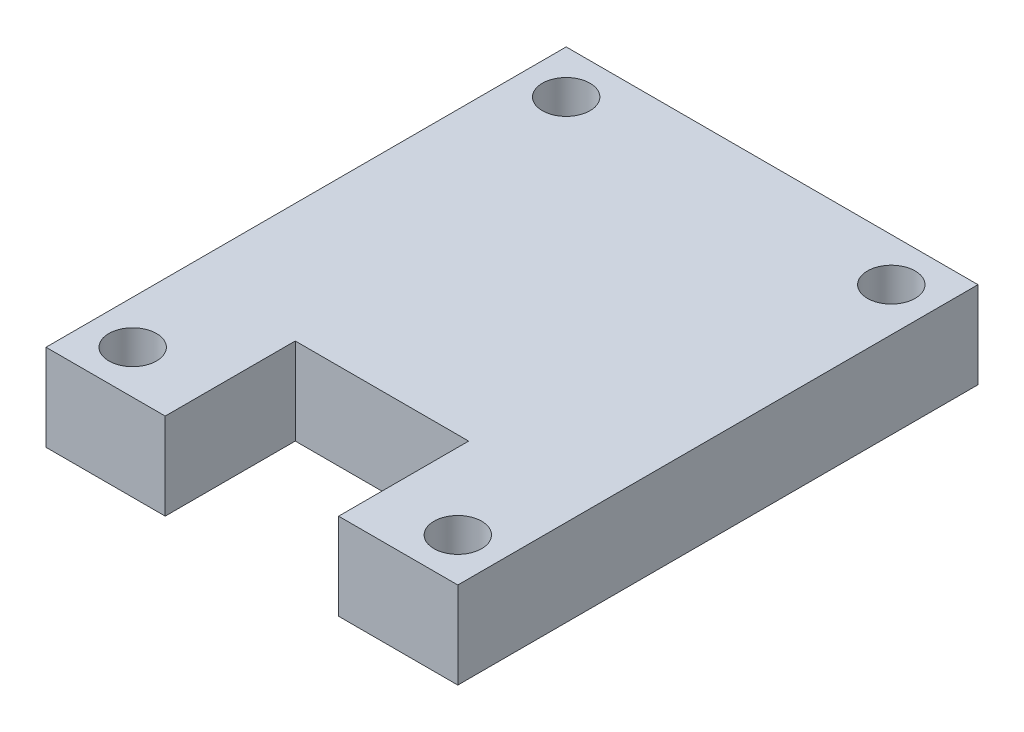
SolidWorks part; units mm, degrees
ref_plane "Plan de face" through (0, 0, 0) normal (0, 0, 1) x (1, 0, 0)
ref_plane "Plan de dessus" through (0, 0, 0) normal (0, 1, 0) x (1, 0, 0)
ref_plane "Plan de droite" through (0, 0, 0) normal (1, 0, 0) x (0, 0, -1)
sketch "Esquisse1" plane through (0, 0, 0) normal (0, 1, 0) x (1, 0, 0)
  line L0 (0, 0) -> (38, 0)
  line L1 (38, 0) -> (38, 48)
  line L2 (38, 48) -> (0, 48)
  line L3 (0, 48) -> (0, 0)
extrude "Boss.-Extru.1" add sketch "Esquisse1" along normal blind 8
sketch "Esquisse3" plane through (0, 0, 0) normal (0, -1, 0) x (1, 0, 0)
  line L0 (0, 0) -> (8, 0) construction
  line L1 (0, 0) -> (38, 0) construction
  line L2 (8, 0) -> (8, -8) construction
  line L3 (8, -8) -> (0, 0) construction
  line L4 (0, 0) -> (8, 0) construction
  line L5 (8, 0) -> (0, -8) construction
  line L6 (0, -48) -> (0, 0) construction
  line L7 (0, -8) -> (0, -48) construction
  line L8 (38, -48) -> (0, -48) construction
  line L9 (0, -48) -> (8, -48) construction
  line L10 (8, -48) -> (8, -40) construction
  line L11 (8, -40) -> (0, -48) construction
  line L12 (0, -48) -> (8, -48) construction
  line L13 (8, -48) -> (0, -40) construction
  line L14 (38, 0) -> (38, -8) construction
  line L15 (38, 0) -> (38, -48) construction
  line L16 (38, -8) -> (30, -8) construction
  line L17 (30, -8) -> (30, 0) construction
  line L18 (30, -8) -> (38, 0) construction
  line L19 (38, 0) -> (30, 0) construction
  line L20 (30, 0) -> (38, -8) construction
  line L21 (38, -8) -> (38, -48) construction
  line L22 (38, -48) -> (30, -48) construction
  line L23 (30, -48) -> (30, -40) construction
  line L24 (30, -40) -> (38, -48) construction
  line L25 (38, -48) -> (30, -48) construction
  line L26 (30, -48) -> (38, -40) construction
  line L27 (38, -40) -> (30, -40) construction
  circle A0 centre (4, -4) radius 2.2
  circle A1 centre (34, -4) radius 2.2
  circle A2 centre (34, -44) radius 2.2
  circle A3 centre (4, -44) radius 2.2
extrude "Enlèv. mat.-Extru.1" cut sketch "Esquisse3" against normal blind 8
sketch "Esquisse5" plane through (0, 8, 0) normal (0, 1, 0) x (1, 0, 0)
  line L0 (0, 0) -> (38, 0) construction
  line L1 (38, 0) -> (19, 0) construction
  line L2 (19, 0) -> (19, 12) construction
  line L3 (19, 12) -> (27, 12)
  line L4 (27, 12) -> (27, 0)
  line L5 (27, 0) -> (11, 0)
  line L6 (11, 0) -> (11, 12)
  line L7 (11, 12) -> (19, 12)
extrude "Enlèv. mat.-Extru.2" cut sketch "Esquisse5" against normal blind 8
